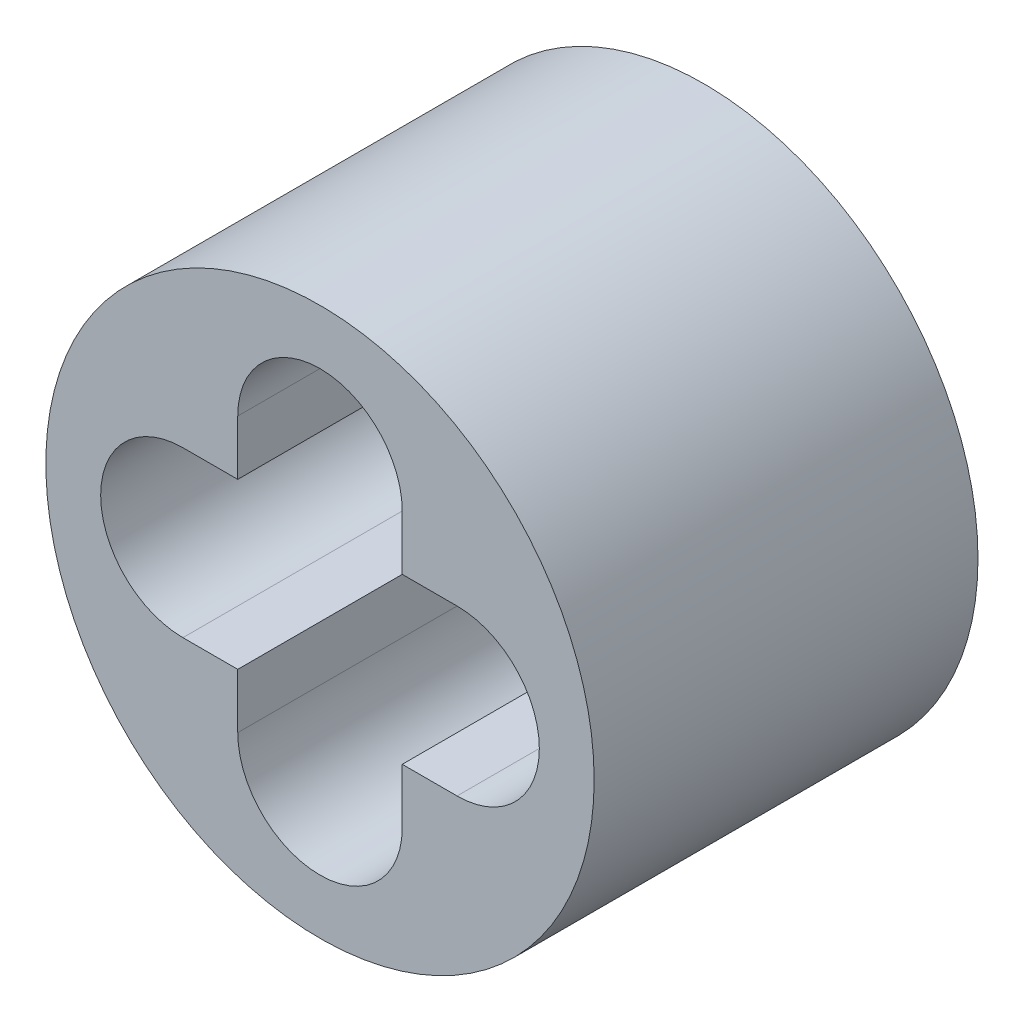
SolidWorks part; units mm, degrees
ref_plane "Front Plane" through (0, 0, 0) normal (0, 0, 1) x (1, 0, 0)
ref_plane "Top Plane" through (0, 0, 0) normal (0, 1, 0) x (1, 0, 0)
ref_plane "Right Plane" through (0, 0, 0) normal (1, 0, 0) x (0, 0, -1)
sketch "Sketch1" plane through (0, 0, 0) normal (0, 0, 1) x (1, 0, 0)
  line L0 (-2.5, 0) -> (2.5, 0) construction
  line L1 (-2.5, 1.5) -> (-1.5, 1.5)
  line L2 (-2.5, -1.5) -> (-1.5, -1.5)
  line L3 (0, 2.5) -> (0, -2.5) construction
  line L4 (1.5, 2.5) -> (1.5, 1.5)
  line L5 (-1.5, 2.5) -> (-1.5, 1.5)
  line L6 (1.5, 1.5) -> (2.5, 1.5)
  line L7 (-1.5, -1.5) -> (-1.5, -2.5)
  line L8 (1.5, -1.5) -> (2.5, -1.5)
  line L9 (1.5, -1.5) -> (1.5, -2.5)
  circle A0 centre (0, 0) radius 4 construction
  arc A1 (-2.5, 1.5) -> (-2.5, -1.5) centre (-2.5, 0) ccw
  arc A2 (2.5, -1.5) -> (2.5, 1.5) centre (2.5, 0) ccw
  arc A3 (1.5, 2.5) -> (-1.5, 2.5) centre (0, 2.5) ccw
  arc A4 (-1.5, -2.5) -> (1.5, -2.5) centre (0, -2.5) ccw
  circle A5 centre (0, 0) radius 5
  point P5 (0, 0)
  point P6 (0, 0)
  point P13 (0, 0)
  dimension "D1" = 8
  dimension "D3" = 10
  dimension "D2" = 3
extrude "Boss-Extrude1" add sketch "Sketch1" along normal blind 7
